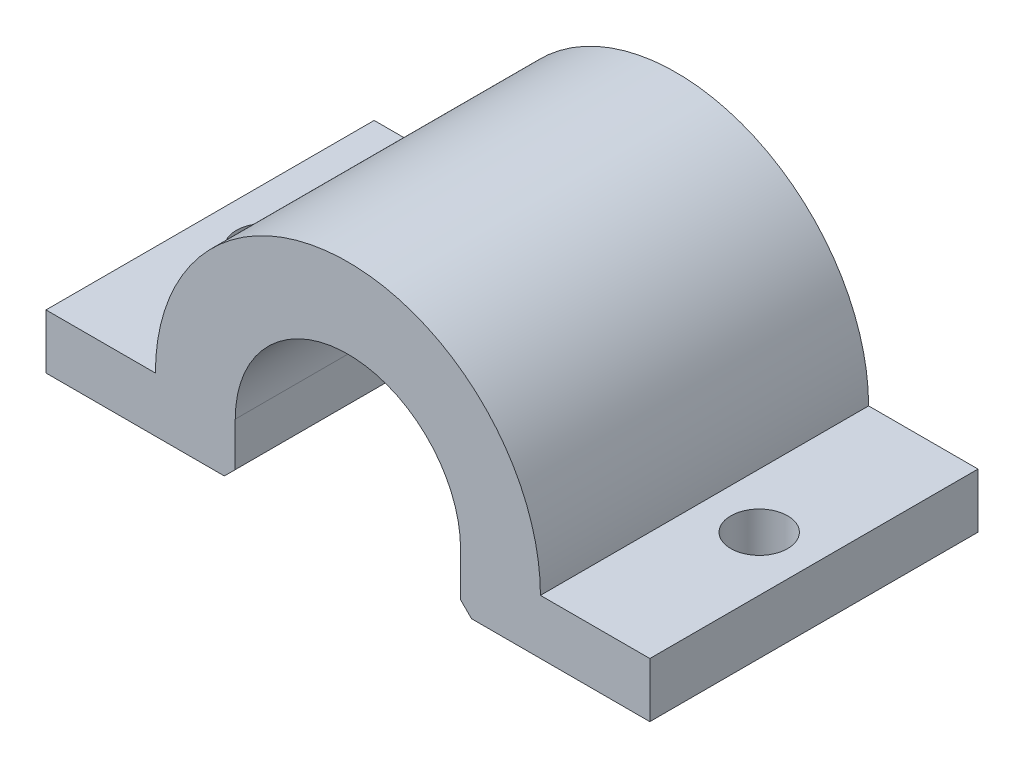
SolidWorks part; units mm, degrees
ref_plane "Plan de face" through (0, 0, 0) normal (0, 0, 1) x (1, 0, 0)
ref_plane "Plan de dessus" through (0, 0, 0) normal (0, 1, 0) x (1, 0, 0)
ref_plane "Plan de droite" through (0, 0, 0) normal (1, 0, 0) x (0, 0, -1)
sketch "Esquisse1" plane through (0, 0, 0) normal (0, 0, 1) x (1, 0, 0)
  line L0 (-27.6, 0) -> (-17.6, 0)
  line L2 (10.3, 0) -> (10.3, -5)
  line L3 (10.3, -5) -> (27.6, -5)
  line L4 (27.6, 0) -> (27.6, -5)
  line L6 (-10.3, 0) -> (-10.3, -5)
  line L7 (-10.3, -5) -> (-27.6, -5)
  line L8 (-27.6, 0) -> (-27.6, -5)
  line L10 (17.6, 0) -> (27.6, 0)
  arc A0 (-10.3, 0) -> (10.3, 0) centre (0, 0) cw
  arc A1 (-17.6, 0) -> (17.6, 0) centre (0, 0) cw
  dimension "D1" = 5
  dimension "D2" = 17.3
  dimension "D3" = 10.3
  dimension "D4" = 17.6
extrude "Boss.-Extru.1" add sketch "Esquisse1" along normal blind 30
sketch "Esquisse3" plane through (0, 0, 0) normal (0, 1, 0) x (1, 0, 0)
  line L0 (-27.6, 0) -> (-17.6, -30) construction
  line L1 (-17.6, 0) -> (-27.6, -30) construction
  line L2 (17.6, 0) -> (27.6, -30) construction
  line L3 (27.6, 0) -> (17.6, -30) construction
  circle A0 centre (-22.6, -15) radius 2.6
  circle A1 centre (22.6, -15) radius 2.6
  dimension "D1" = 5.2
extrude "Enlèv. mat.-Extru.1" cut sketch "Esquisse3" against normal through all
chamfer "Chanfrein1" distance 1 angle 45 2 edges at (10.3, -5, 15) (-10.3, -5, 15)
